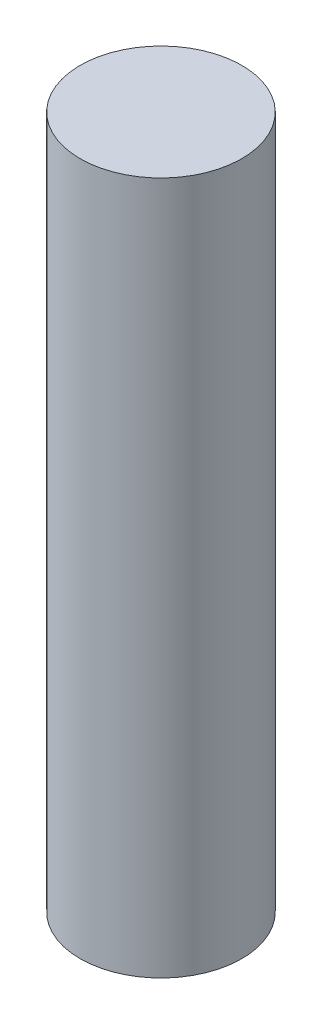
SolidWorks part; units mm, degrees
ref_plane "Front" through (0, 0, 0) normal (0, 0, 1) x (1, 0, 0)
ref_plane "Top" through (0, 0, 0) normal (0, 1, 0) x (1, 0, 0)
ref_plane "Right" through (0, 0, 0) normal (1, 0, 0) x (0, 0, -1)
sketch "Sketch1" plane through (0, 0, 0) normal (0, 1, 0) x (1, 0, 0)
  circle A0 centre (0, 0) radius 3.5
  dimension "D1" = 7
extrude "Boss-Extrude1" add sketch "Sketch1" along normal blind 30
